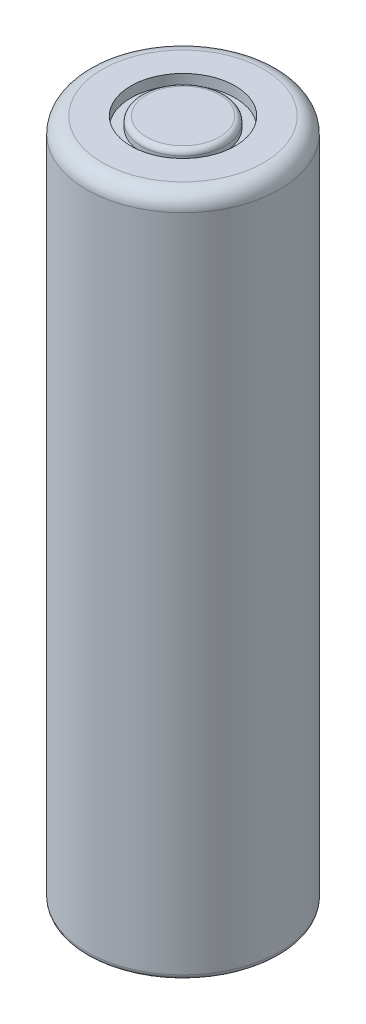
SolidWorks part; units mm, degrees
material "Verzinkter Stahl"
ref_plane "Ebene vorne" through (0, 0, 0) normal (0, 0, 1) x (1, 0, 0)
ref_plane "Ebene oben" through (0, 0, 0) normal (0, 1, 0) x (1, 0, 0)
ref_plane "Ebene rechts" through (0, 0, 0) normal (1, 0, 0) x (0, 0, -1)
sketch "Skizze1" plane through (0, 0, 0) normal (0, 1, 0) x (1, 0, 0)
  circle A0 centre (0, 0) radius 9.25
  dimension "D1" = 18.5
extrude "Aufsatz-Linear austragen1" add sketch "Skizze1" along normal blind 65.3
fillet "Verrundung1" radius 1.5 1 edges at (0, 65.3, 9.25)
fillet "Verrundung2" radius 0.5 1 edges at (0, 0, 9.25)
sketch "Skizze2" plane through (0, 65.3, 0) normal (0, 1, 0) x (1, 0, 0)
  circle A0 centre (0, 0) radius 5
  circle A1 centre (0, 0) radius 4
  dimension "D1" = 10
  dimension "D2" = 8
extrude "Schnitt-Linear austragen1" cut sketch "Skizze2" against normal blind 1
fillet "Verrundung3" radius 0.5 1 edges at (0, 65.3, 4)
